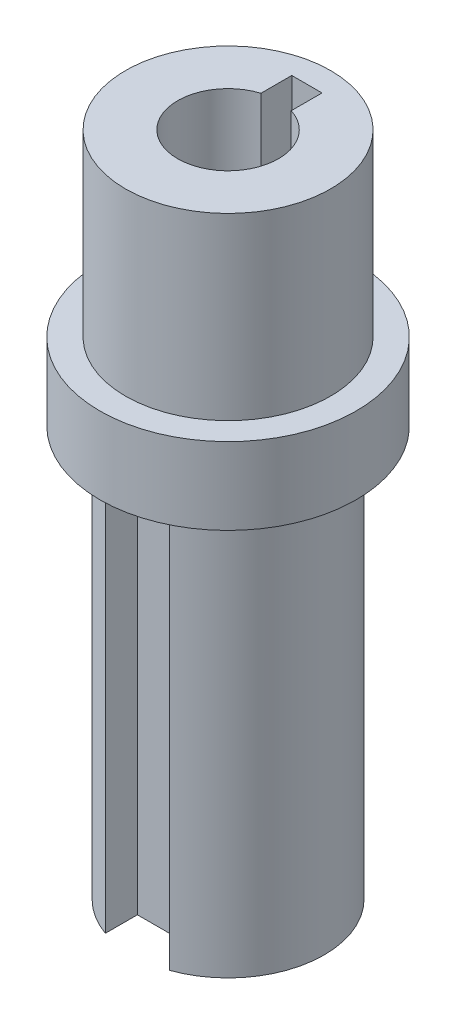
SolidWorks part; units mm, degrees
other "Markup1"
sketch "Sketch3" plane through (12.7, 0, 12.7) normal (0.3237, 0.0352, 0.9455) x (0.9458, 0.0158, -0.3244)
ref_plane "Front Plane" through (0, 0, 0) normal (0, 0, 1) x (1, 0, 0)
ref_plane "Top Plane" through (0, 0, 0) normal (0, 1, 0) x (1, 0, 0)
ref_plane "Right Plane" through (0, 0, 0) normal (1, 0, 0) x (0, 0, -1)
curve "ImportedCurve1"
curve "ImportedCurve2"
curve "ImportedCurve3"
curve "ImportedCurve4"
curve "ImportedCurve5"
curve "ImportedCurve6"
curve "ImportedCurve7"
curve "ImportedCurve8"
curve "ImportedCurve9"
curve "ImportedCurve10"
curve "ImportedCurve11"
curve "ImportedCurve12"
curve "ImportedCurve13"
curve "ImportedCurve14"
curve "ImportedCurve15"
curve "ImportedCurve16"
curve "ImportedCurve17"
curve "ImportedCurve18"
curve "ImportedCurve19"
curve "ImportedCurve20"
sketch "Sketch2" plane through (0, 0, 0) normal (0, 0, 1) x (1, 0, 0)
  line L0 (-10.16, 0) -> (-4.9911, 0)
  line L1 (-4.9911, 0) -> (-10.16, 0) construction
  line L2 (-4.9911, 0) -> (-4.9911, -34.29) construction
  line L3 (-4.9911, 0) -> (-4.9911, -34.29)
  line L4 (-2.032, -34.29) -> (-4.9911, -34.29) construction
  line L5 (-4.9911, -34.29) -> (-2.032, -34.29)
  line L6 (-2.032, -34.29) -> (-2.032, -66.04) construction
  line L7 (-2.032, -34.29) -> (-2.032, -66.04)
  line L8 (-2.032, -66.04) -> (-9.525, -66.04)
  line L9 (-9.525, -25.4) -> (-9.525, -66.04) construction
  line L10 (-9.525, -66.04) -> (-9.525, -25.4)
  line L11 (-9.525, -25.4) -> (-12.7, -25.4)
  line L12 (-9.525, -25.4) -> (-12.7, -25.4) construction
  line L13 (-12.7, -25.4) -> (-12.7, -17.78)
  line L14 (-12.7, -17.78) -> (-12.7, -25.4) construction
  line L15 (-10.16, -17.78) -> (-12.7, -17.78) construction
  line L16 (-12.7, -17.78) -> (-10.16, -17.78)
  line L17 (-10.16, 0) -> (-10.16, -17.78) construction
  line L18 (-10.16, -17.78) -> (-10.16, 0)
  line L19 (0, 0) -> (0, -66.04) construction
  line L30 (-2.032, -66.04) -> (-9.525, -66.04) construction
revolve "Revolve1" add sketch "Sketch2" angle 360 about L19
sketch "Sketch4" plane through (0, 0, 0) normal (0, 1, 0) x (1, 0, 0)
  line L0 (0, 7.81) -> (0, 10.16) construction
  line L2 (1.5, 4.7604) -> (1.5, 7.81)
  line L3 (1.5, 7.81) -> (-1.5, 7.81)
  line L4 (-1.5, 4.7604) -> (-1.5, 7.81)
  circle A0 centre (0, 0) radius 4.9911 construction
  arc A2 (-1.5, 4.7604) -> (1.5, 4.7604) centre (0, 0) cw
  circle A3 centre (0, 0) radius 4.9911 construction
  circle A4 centre (0, 0) radius 10.16 construction
  dimension "D1" = 2.35
  dimension "D2" = 3
extrude "Cut-Extrude1" cut sketch "Sketch4" against normal blind 21.8
sketch "Sketch5" plane through (0, -66.04, 0) normal (0, -1, 0) x (1, 0, 0)
  line L0 (-3.175, 8.9803) -> (-3.175, 5.8053)
  line L1 (-3.175, 5.8053) -> (3.175, 5.8053)
  line L2 (3.175, 5.8053) -> (3.175, 8.9803)
  circle A0 centre (0, 0) radius 9.525 construction
  arc A1 (-3.175, 8.9803) -> (3.175, 8.9803) centre (0, 0) cw
  point P4 (0, 5.8053)
  dimension "D1" = 6.35
  dimension "D2" = 3.175
extrude "Cut-Extrude2" cut sketch "Sketch5" against normal blind 39.37
